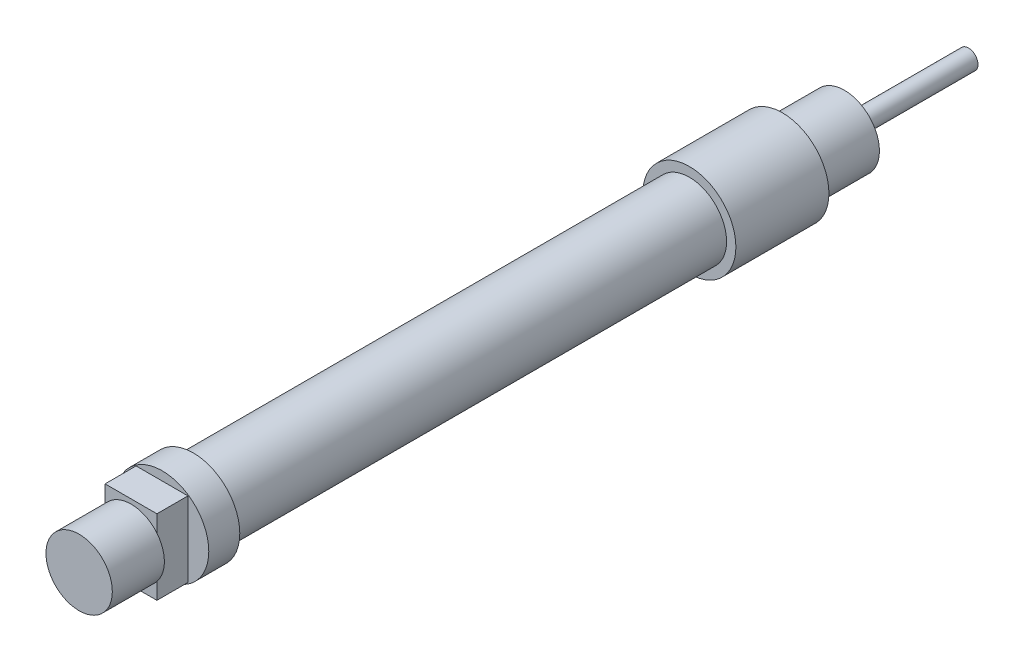
SolidWorks part; units mm, degrees
ref_plane "Alzado" through (0, 0, 0) normal (0, 0, 1) x (1, 0, 0)
ref_plane "Planta" through (0, 0, 0) normal (0, 1, 0) x (1, 0, 0)
ref_plane "Vista lateral" through (0, 0, 0) normal (1, 0, 0) x (0, 0, -1)
sketch "Croquis1" plane through (0, 0, 0) normal (0, 0, 1) x (1, 0, 0)
  circle A0 centre (-11.6703, 4.9904) radius 7.5
extrude "Saliente-Extruir1" add sketch "Croquis1" along normal blind 15
sketch "Croquis2" plane through (0, 0, 15) normal (0, 0, 1) x (1, 0, 0)
  line L0 (-11.6703, 12.4904) -> (-11.6703, 10.9904)
  circle A0 centre (-11.6703, 4.9904) radius 7.5 construction
  circle A1 centre (-11.6703, 4.9904) radius 6
extrude "Saliente-Extruir2" add sketch "Croquis2" along normal blind 80 contours A1
sketch "Croquis3" plane through (0, 0, 15) normal (0, 0, 1) x (1, 0, 0)
  line L0 (-17.6703, 4.9904) -> (-11.6703, 4.9904)
  circle A0 centre (-11.6703, 4.9904) radius 6 construction
  point P5 (-8.2567, 12.024)
sketch "Croquis4" plane through (0, 0, 95) normal (0, 0, 1) x (1, 0, 0)
  circle A0 centre (-11.6581, 5.0025) radius 7.5
extrude "Saliente-Extruir3" add sketch "Croquis4" along normal blind 5
sketch "Croquis5" plane through (0, 0, 100) normal (0, 0, 1) x (1, 0, 0)
  line L2 (-7.5188, 4.9904) -> (-7.5188, 11.0668)
  line L3 (-7.5188, 11.0668) -> (-15.8771, 11.0668)
  line L4 (-15.8771, 11.0668) -> (-15.8771, -1.0233)
  line L5 (-15.8771, -1.0233) -> (-7.5188, -1.0233)
  line L6 (-7.5188, -1.0233) -> (-7.5188, 4.9904)
extrude "Saliente-Extruir4" add sketch "Croquis5" along normal blind 5
sketch "Croquis6" plane through (-7.5188, 0, 0) normal (1, 0, 0) x (0, 0, -1)
  line L0 (-105, -1.0233) -> (-105, 11.0668) construction
  line L1 (-105, 11.0668) -> (-105, -1.0233)
  arc A0 (-105, 11.0668) -> (-105, -1.0233) centre (-105, 5.0218) ccw
sketch "Croquis7" plane through (0, 0, 105) normal (0, 0, 1) x (1, 0, 0)
  circle A0 centre (-11.6703, 4.9904) radius 5.35
  point P3 (-15.6914, 7.4364)
extrude "Saliente-Extruir6" add sketch "Croquis7" along normal blind 8.39
sketch "Croquis8" plane through (0, 0, 0) normal (0, 0, -1) x (-1, 0, 0)
  circle A0 centre (11.6703, 4.9904) radius 5.6412
extrude "Saliente-Extruir7" add sketch "Croquis8" along normal blind 10
sketch "Croquis9" plane through (0, 0, -10) normal (0, 0, -1) x (-1, 0, 0)
  circle A0 centre (11.6703, 4.9904) radius 1.5405
extrude "Saliente-Extruir8" add sketch "Croquis9" along normal blind 20
